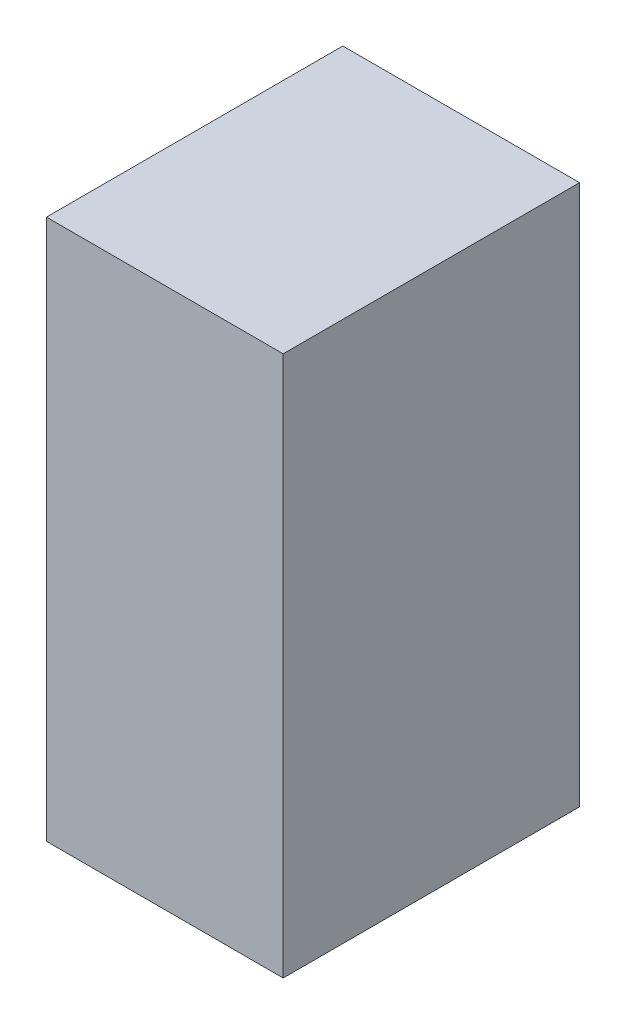
SolidWorks part; units mm, degrees
ref_plane "Front Plane" through (0, 0, 0) normal (0, 0, 1) x (1, 0, 0)
ref_plane "Top Plane" through (0, 0, 0) normal (0, 1, 0) x (1, 0, 0)
ref_plane "Right Plane" through (0, 0, 0) normal (1, 0, 0) x (0, 0, -1)
sketch "Sketch1" plane through (0, 0, 0) normal (0, 1, 0) x (1, 0, 0)
  line L1 (-12.7, 15.9) -> (12.7, 15.9)
  line L2 (-12.7, 15.9) -> (-12.7, -15.9)
  line L3 (-12.7, -15.9) -> (12.7, -15.9)
  line L4 (12.7, 15.9) -> (12.7, -15.9)
  line L5 (-12.7, 15.9) -> (12.7, -15.9) construction
  line L6 (-12.7, -15.9) -> (12.7, 15.9) construction
  point P0 (0, 0)
extrude "Boss-Extrude1" add sketch "Sketch1" along normal blind 58
